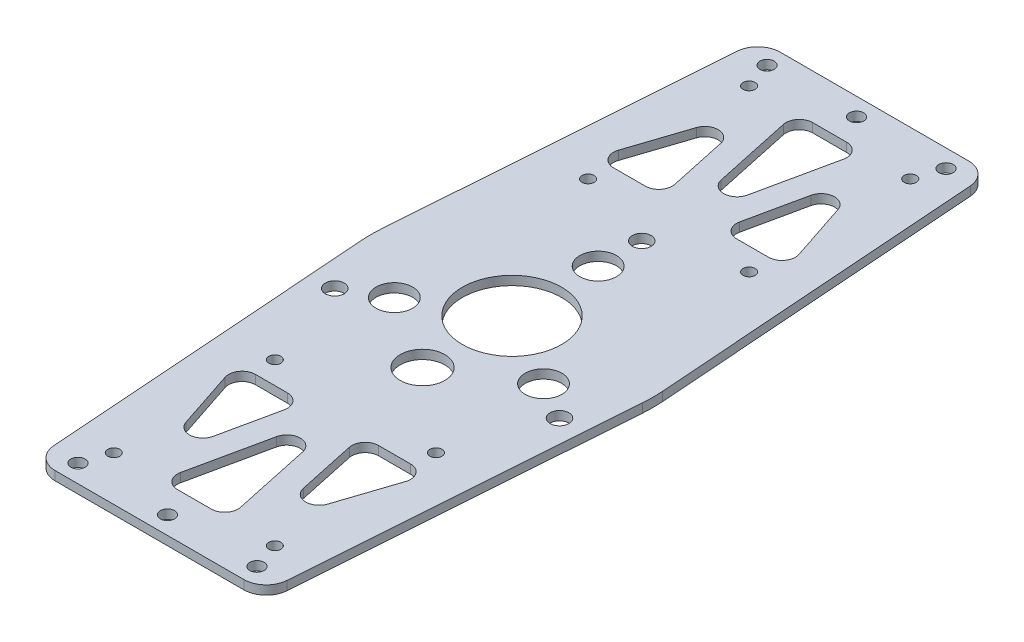
SolidWorks part; units mm, degrees
material "Thornel Mat VMA1"
ref_plane "前视基准面" through (0, 0, 0) normal (0, 0, 1) x (1, 0, 0)
ref_plane "上视基准面" through (0, 0, 0) normal (0, 1, 0) x (1, 0, 0)
ref_plane "右视基准面" through (0, 0, 0) normal (1, 0, 0) x (0, 0, -1)
sketch "草图1" plane through (0, 0, 0) normal (0, 1, 0) x (1, 0, 0)
  line L0 (-75, 90) -> (-70, 90) construction
  line L1 (-75, 90) -> (75, 90)
  line L2 (-75, 90) -> (-75, -90)
  line L3 (-75, -90) -> (75, -90)
  line L4 (75, 90) -> (75, -90)
  line L5 (0, -90) -> (0, 90) construction
  line L6 (-75, 0) -> (75, 0) construction
  line L7 (-70, 90) -> (-70, 85) construction
  line L8 (-70, 85) -> (-50, 85) construction
  line L9 (-70, 85) -> (-70, 65) construction
  circle A0 centre (-70, 85) radius 2.1
  circle A1 centre (-50, 85) radius 2.1
  circle A2 centre (-50, 65) radius 2.1
  circle A3 centre (-70, 65) radius 2.1
  circle A4 centre (70, 65) radius 2.1
  circle A5 centre (50, 65) radius 2.1
  circle A6 centre (50, 85) radius 2.1
  circle A7 centre (70, 85) radius 2.1
  circle A8 centre (70, -85) radius 2.1
  circle A9 centre (50, -85) radius 2.1
  circle A10 centre (50, -65) radius 2.1
  circle A11 centre (70, -65) radius 2.1
  circle A12 centre (-70, -65) radius 2.1
  circle A13 centre (-50, -65) radius 2.1
  circle A14 centre (-50, -85) radius 2.1
  circle A15 centre (-70, -85) radius 2.1
  point P0 (0, 0)
  dimension "D4" = 4.2
  dimension "D9" = 150
  dimension "D1" = 180
  dimension "D2" = 5
  dimension "D3" = 5
  dimension "D7" = 20
  dimension "D8" = 20
  dimension "D5" = 2
  dimension "D6" = 2
extrude "凸台-拉伸1" add sketch "草图1" along normal blind 2
sketch "草图2" plane through (0, 2, 0) normal (0, 1, 0) x (1, 0, 0)
  line L0 (0, 0) -> (0, 29) construction
  line L1 (0, 0) -> (25.1147, -14.5) construction
  line L2 (0, 0) -> (0, 19.25) construction
  line L3 (0, 19.25) -> (0, 0) construction
  line L4 (0, 0) -> (16.671, -9.625) construction
  line L5 (0, 0) -> (0, -20) construction
  circle A0 centre (0, 0) radius 11.1
  circle A1 centre (0, 29) radius 2.1
  circle A2 centre (25.1147, -14.5) radius 2.1
  circle A3 centre (-25.1147, -14.5) radius 2.1
  circle A4 centre (0, 19.25) radius 4.1
  circle A5 centre (16.671, -9.625) radius 4.1
  circle A6 centre (-16.671, -9.625) radius 4.1
  circle A7 centre (0, -20) radius 5
  dimension "D1" = 22.2
  dimension "D3" = 4.2
  dimension "D8" = 8.2
  dimension "D13" = 10
  dimension "D2" = 29
  dimension "D5" = 29
  dimension "D6" = 120
  dimension "D7" = 19.25
  dimension "D10" = 19.25
  dimension "D11" = 19.25
  dimension "D12" = 20
  dimension "D4" = 3
  dimension "D9" = 3
extrude "切除-拉伸1" cut sketch "草图2" against normal blind 2
sketch "草图3" plane through (0, 2, 0) normal (0, 1, 0) x (1, 0, 0)
  line L0 (-75, 60) -> (75, 60) construction
  line L1 (-75, 90) -> (-75, -90) construction
  line L2 (75, -90) -> (75, 90) construction
  line L3 (75, -60) -> (-75, -60) construction
  line L4 (75, 90) -> (-75, 90) construction
  line L5 (-75, -90) -> (75, -90) construction
  line L6 (0, 0) -> (0, 90) construction
  line L7 (0, 0) -> (-75, 0) construction
  line L8 (-20, 77) -> (0, 77) construction
  line L9 (-31.418, 2.2713) -> (-25.7265, 81) construction
  line L10 (-31.418, -2.2713) -> (-25.7265, -81) construction
  line L11 (31.418, -2.2713) -> (25.7265, -81) construction
  line L12 (31.418, 2.2713) -> (25.7265, 81) construction
  line L13 (-25.7265, 81) -> (25.7265, 81) construction
  line L14 (25.7265, -81) -> (-25.7265, -81) construction
  circle A0 centre (-20, 77) radius 1.6
  circle A1 centre (0, 77) radius 1.6
  circle A2 centre (20, 77) radius 1.6
  circle A3 centre (20, -77) radius 1.6
  circle A4 centre (0, -77) radius 1.6
  circle A5 centre (-20, -77) radius 1.6
  circle A6 centre (0, 0) radius 31.5 construction
  arc A7 (-31.418, 2.2713) -> (-31.418, -2.2713) centre (0, 0) ccw construction
  arc A8 (31.418, 2.2713) -> (31.418, -2.2713) centre (0, 0) cw construction
  dimension "D3" = 3.2
  dimension "D4" = 154
  dimension "D7" = 63
  dimension "D10" = 6
  dimension "D9" = 4
  dimension "D1" = 30
  dimension "D2" = 30
  dimension "D6" = 20
  dimension "D8" = 4
  dimension "D5" = 3
extrude "切除-拉伸2" cut sketch "草图3" against normal through all
sketch "草图4" plane through (0, 2, 0) normal (0, 1, 0) x (1, 0, 0)
  line L0 (25.7265, -81) -> (-25.7265, -81) construction
  line L1 (-31.418, -2.2713) -> (-25.7265, -81) construction
  line L2 (31.418, -2.2713) -> (25.7265, -81) construction
  line L3 (31.418, 2.2713) -> (25.7265, 81) construction
  line L4 (-31.418, 2.2713) -> (-25.7265, 81) construction
  line L5 (-25.7265, 81) -> (25.7265, 81) construction
  line L6 (25.7265, -81) -> (-25.7265, -81)
  line L7 (-31.418, -2.2713) -> (-25.7265, -81)
  line L8 (31.418, -2.2713) -> (25.7265, -81)
  line L9 (31.418, 2.2713) -> (25.7265, 81)
  line L10 (-31.418, 2.2713) -> (-25.7265, 81)
  line L11 (-25.7265, 81) -> (25.7265, 81)
  line L13 (-75, 90) -> (75, 90)
  line L14 (-75, 90) -> (-75, -90)
  line L15 (-75, -90) -> (75, -90)
  line L16 (75, 90) -> (75, -90)
  line L17 (0, -90) -> (0, 90) construction
  line L18 (-75, 0) -> (75, 0) construction
  circle A0 centre (0, 0) radius 31.5 construction
  circle A1 centre (0, 0) radius 31.5 construction
  arc A2 (-31.418, 2.2713) -> (-31.418, -2.2713) centre (0, 0) ccw
  arc A3 (31.418, 2.2713) -> (31.418, -2.2713) centre (0, 0) cw
extrude "切除-拉伸3" cut sketch "草图4" against normal through all
fillet "圆角1" radius 5 4 edges at (-25.7265, 1, 81) (25.7265, 1, 81) (25.7265, 1, -81) (-25.7265, 1, -81)
sketch "草图5" plane through (0, 2, 0) normal (0, 1, 0) x (1, 0, 0)
  line L0 (-21.474, -28.8735) -> (-19.425, -57.2163)
  line L1 (-16.4328, -60) -> (16.4328, -60)
  line L2 (19.425, -57.2163) -> (21.474, -28.8735)
  line L4 (26.0619, -76.3605) -> (31.418, -2.2713) construction
  line L5 (-31.418, -2.2713) -> (-26.0619, -76.3605) construction
  line L6 (-21.0749, -81) -> (21.0749, -81) construction
  line L7 (0, 0) -> (0, 77) construction
  line L8 (-7.4049, 60) -> (-16.9341, 60)
  line L9 (-19.9263, 57.2163) -> (-23.2611, 11.0869)
  line L11 (-9.1866, 19.1432) -> (-4.4288, 56.6222)
  line L13 (-26.0619, 76.3605) -> (-31.418, 2.2713) construction
  line L14 (21.0749, 81) -> (-21.0749, 81) construction
  line L15 (19.9263, 57.2163) -> (23.2611, 11.0869)
  line L16 (7.4049, 60) -> (16.9341, 60)
  line L17 (9.1866, 19.1432) -> (4.4288, 56.6222)
  arc A0 (-16.8558, -26.136) -> (16.8558, -26.136) centre (0, 0) ccw
  circle A1 centre (0, 0) radius 11.1 construction
  arc A2 (16.4328, -60) -> (19.425, -57.2163) centre (16.4328, -57) ccw
  arc A3 (21.474, -28.8735) -> (16.8558, -26.136) centre (18.4818, -28.6572) ccw
  arc A4 (-21.474, -28.8735) -> (-16.8558, -26.136) centre (-18.4818, -28.6572) cw
  arc A5 (-19.425, -57.2163) -> (-16.4328, -60) centre (-16.4328, -57) ccw
  circle A6 centre (0, 19.25) radius 4.1 construction
  arc A7 (-17.6252, 9.4527) -> (-10.5763, 16.9748) centre (0, 0) cw
  arc A8 (-16.9341, 60) -> (-19.9263, 57.2163) centre (-16.9341, 57) ccw
  arc A9 (-7.4049, 60) -> (-4.4288, 56.6222) centre (-7.4049, 57) cw
  arc A10 (-10.5763, 16.9748) -> (-9.1866, 19.1432) centre (-12.1627, 19.521) ccw
  arc A11 (-23.2611, 11.0869) -> (-17.6252, 9.4527) centre (-20.2689, 10.8706) ccw
  arc A12 (17.6252, 9.4527) -> (10.5763, 16.9748) centre (0, 0) ccw
  arc A13 (23.2611, 11.0869) -> (17.6252, 9.4527) centre (20.2689, 10.8706) cw
  arc A14 (16.9341, 60) -> (19.9263, 57.2163) centre (16.9341, 57) cw
  arc A15 (7.4049, 60) -> (4.4288, 56.6222) centre (7.4049, 57) ccw
  arc A16 (10.5763, 16.9748) -> (9.1866, 19.1432) centre (12.1627, 19.521) cw
  point P42 (-4, 60)
  dimension "D3" = 20
  dimension "D5" = 3
  dimension "D8" = 5
  dimension "D10" = 3
  dimension "D11" = 20
  dimension "D1" = 8
  dimension "D2" = 21
  dimension "D4" = 8
  dimension "D6" = 7.5
  dimension "D7" = 4
  dimension "D9" = 21
extrude "切除-拉伸4" [suppressed] cut sketch "草图5" against normal through all
sketch "草图6" plane through (0, 2, 0) normal (0, 1, 0) x (1, 0, 0)
  line L0 (0, 0) -> (31.5, 0) construction
  line L1 (-20, 77) -> (20, 77) construction
  line L2 (-20, 81) -> (20, 81)
  line L3 (-20, 73) -> (20, 73)
  line L4 (-20, -77) -> (20, -77) construction
  line L5 (-20, -81) -> (20, -81)
  line L6 (-20, -73) -> (20, -73)
  arc A0 (31.418, -2.2713) -> (31.418, 2.2713) centre (0, 0) ccw construction
  arc A1 (-20, 81) -> (-20, 73) centre (-20, 77) ccw
  arc A2 (20, 73) -> (20, 81) centre (20, 77) ccw
  circle A3 centre (20, 77) radius 1.6 construction
  circle A4 centre (0, 77) radius 1.6 construction
  circle A5 centre (-20, 77) radius 1.6 construction
  circle A6 centre (20, 77) radius 1.6
  circle A7 centre (0, 77) radius 1.6
  circle A8 centre (-20, 77) radius 1.6
  arc A9 (-20, -81) -> (-20, -73) centre (-20, -77) cw
  arc A10 (20, -73) -> (20, -81) centre (20, -77) cw
  circle A11 centre (-20, -77) radius 1.6
  circle A12 centre (20, -77) radius 1.6
  circle A13 centre (0, -77) radius 1.6
  point P8 (0, 77)
  point P26 (0, -77)
  dimension "D1" = 4
extrude "凸台-拉伸2" [suppressed] add sketch "草图6" along normal blind 10 separate body
other "保存实体1"
sketch "草图7" plane through (0, 2, 0) normal (0, 1, 0) x (1, 0, 0)
  line L0 (0, 81) -> (0, -81) construction
  line L1 (21.0749, 81) -> (-21.0749, 81) construction
  line L2 (-21.0749, -81) -> (21.0749, -81) construction
  line L3 (-31.5, 0) -> (-50031.5, 0) construction
  line L4 (-18, -53) -> (18, -53) construction
  line L5 (-18, 71) -> (18, 71) construction
  line L6 (-18, 71) -> (-18, 35) construction
  line L7 (-18, 35) -> (18, 35) construction
  line L8 (18, 71) -> (18, 35) construction
  line L9 (0, 35) -> (0, 71) construction
  line L10 (-18, 53) -> (18, 53) construction
  line L11 (0, -35) -> (0, -71) construction
  line L12 (18, -71) -> (18, -35) construction
  line L13 (-18, -35) -> (18, -35) construction
  line L14 (-18, -71) -> (-18, -35) construction
  line L15 (-18, -71) -> (18, -71) construction
  arc A0 (-31.418, 2.2713) -> (-31.418, -2.2713) centre (0, 0) ccw construction
  circle A1 centre (-18, 71) radius 1.35
  circle A2 centre (18, 71) radius 1.35
  circle A3 centre (18, 35) radius 1.35
  circle A4 centre (-18, 35) radius 1.35
  circle A5 centre (-18, -35) radius 1.35
  circle A6 centre (18, -35) radius 1.35
  circle A7 centre (18, -71) radius 1.35
  circle A8 centre (-18, -71) radius 1.35
  point P11 (-31.5, 0)
  point P12 (0, 53)
  point P32 (0, -53)
  dimension "D3" = 2.7
  dimension "D1" = 36
  dimension "D2" = 28
extrude "切除-拉伸5" cut sketch "草图7" against normal through all
sketch "草图8" plane through (0, 0, 0) normal (0, -1, 0) x (1, 0, 0)
  line L0 (0, 81) -> (0, -81) construction
  line L1 (-21.0749, 81) -> (21.0749, 81) construction
  line L2 (21.0749, -81) -> (-21.0749, -81) construction
  line L3 (-31.5, 0) -> (-50031.5, 0) construction
  line L4 (7.5, 71) -> (-7.5, 71)
  line L5 (-7.5, 71) -> (0, 36)
  line L6 (7.5, 71) -> (0, 36)
  line L7 (-18, 71) -> (18, 71) construction
  line L8 (-12.3749, 67.5) -> (-21.482, 40)
  line L9 (-21.482, 40) -> (-6.482, 40)
  line L10 (-6.482, 40) -> (-12.3749, 67.5)
  line L11 (-18, 35) -> (18, 35) construction
  line L12 (21.482, 40) -> (6.482, 40)
  line L13 (12.3749, 67.5) -> (21.482, 40)
  line L14 (6.482, 40) -> (12.3749, 67.5)
  line L15 (12.3749, -67.5) -> (21.482, -40)
  line L16 (6.482, -40) -> (12.3749, -67.5)
  line L17 (21.482, -40) -> (6.482, -40)
  line L18 (7.5, -71) -> (-7.5, -71)
  line L19 (-7.5, -71) -> (0, -36)
  line L20 (7.5, -71) -> (0, -36)
  line L21 (-21.482, -40) -> (-6.482, -40)
  line L22 (-12.3749, -67.5) -> (-21.482, -40)
  line L23 (-6.482, -40) -> (-12.3749, -67.5)
  arc A0 (-31.418, 2.2713) -> (-31.418, -2.2713) centre (0, 0) ccw construction
  point P11 (-31.5, 0)
  point P16 (0, 71)
  dimension "D1" = 15
  dimension "D2" = 35
  dimension "D3" = 5
  dimension "D4" = 15
  dimension "D5" = 5.5
  dimension "D6" = 3.5
extrude "切除-拉伸6" cut sketch "草图8" against normal through all
fillet "圆角2" radius 3 18 edges at (-7.5, 1, 71) (7.5, 1, 71) (0, 1, 36) (-21.482, 1, -40) (-6.482, 1, -40) (-12.3749, 1, -67.5) (6.482, 1, -40) (21.482, 1, -40) (12.3749, 1, -67.5) (7.5, 1, -71) (-7.5, 1, -71) (0, 1, -36) (21.482, 1, 40) (6.482, 1, 40) (12.3749, 1, 67.5) (-6.482, 1, 40) (-21.482, 1, 40) (-12.3749, 1, 67.5)
